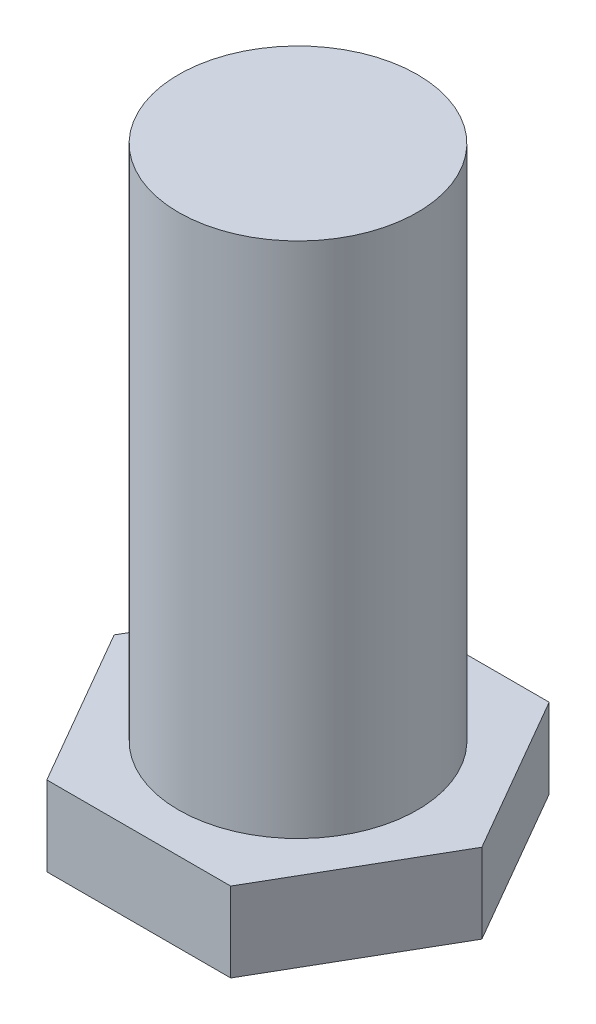
SolidWorks part; units mm, degrees
ref_plane "前基準面" through (0, 0, 0) normal (0, 0, 1) x (1, 0, 0)
ref_plane "上基準面" through (0, 0, 0) normal (0, 1, 0) x (1, 0, 0)
ref_plane "右基準面" through (0, 0, 0) normal (1, 0, 0) x (0, 0, -1)
sketch "草圖1" plane through (0, 0, 0) normal (0, 1, 0) x (1, 0, 0)
  line L1 (4.6188, 0) -> (2.3094, 4)
  line L2 (2.3094, 4) -> (-2.3094, 4)
  line L3 (-2.3094, 4) -> (-4.6188, 0)
  line L4 (-4.6188, 0) -> (-2.3094, -4)
  line L5 (-2.3094, -4) -> (2.3094, -4)
  line L6 (2.3094, -4) -> (4.6188, 0)
  circle A0 centre (0, 0) radius 4 construction
  dimension "D1" = 8
extrude "填料-伸長1" add sketch "草圖1" along normal blind 2
sketch "草圖2" plane through (0, 0, 0) normal (0, 1, 0) x (1, 0, 0)
  circle A0 centre (0, 0) radius 3
  dimension "D1" = 6
extrude "填料-伸長2" add sketch "草圖2" along normal blind 15
